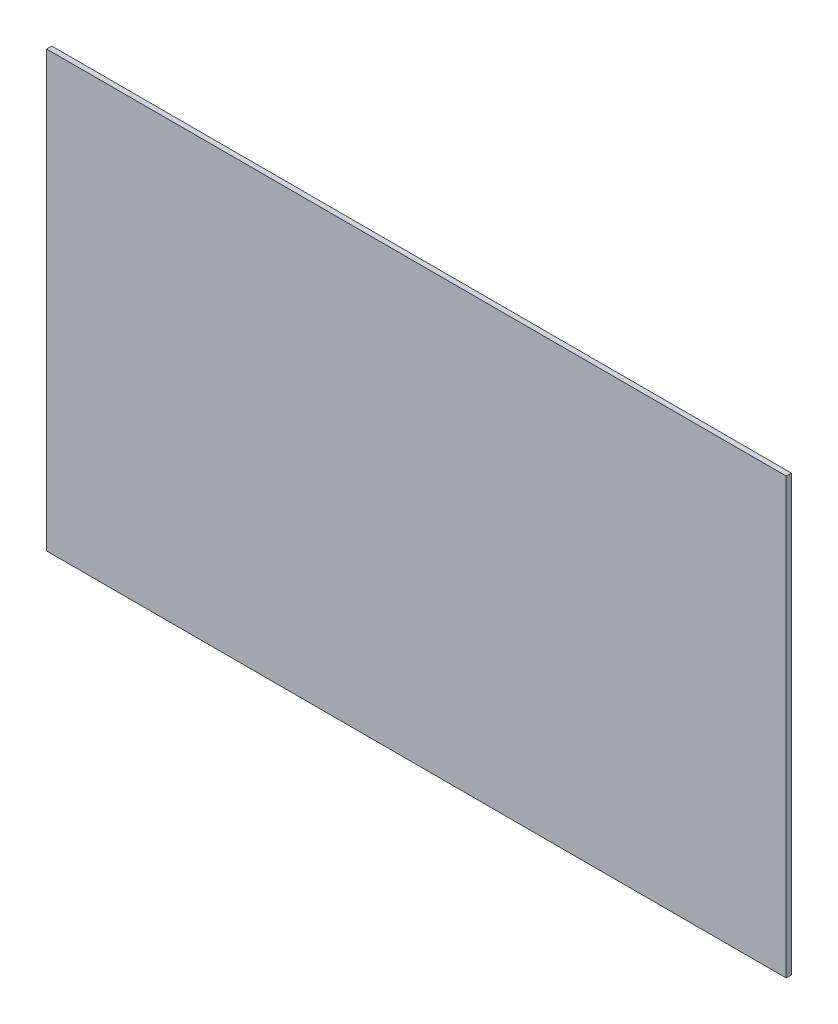
SolidWorks part; units mm, degrees
material "Glass"
ref_plane "Front" through (0, 0, 0) normal (0, 0, 1) x (1, 0, 0)
ref_plane "Top" through (0, 0, 0) normal (0, 1, 0) x (1, 0, 0)
ref_plane "Right" through (0, 0, 0) normal (1, 0, 0) x (0, 0, -1)
sketch "Sketch1" plane through (0, 0, 0) normal (0, 0, 1) x (1, 0, 0)
  line L1 (0, 0) -> (723.9, 0)
  line L2 (0, 0) -> (0, 425.45)
  line L3 (0, 425.45) -> (723.9, 425.45)
  line L4 (723.9, 0) -> (723.9, 425.45)
extrude "Extrude1" add sketch "Sketch1" along normal mid plane 5.08
